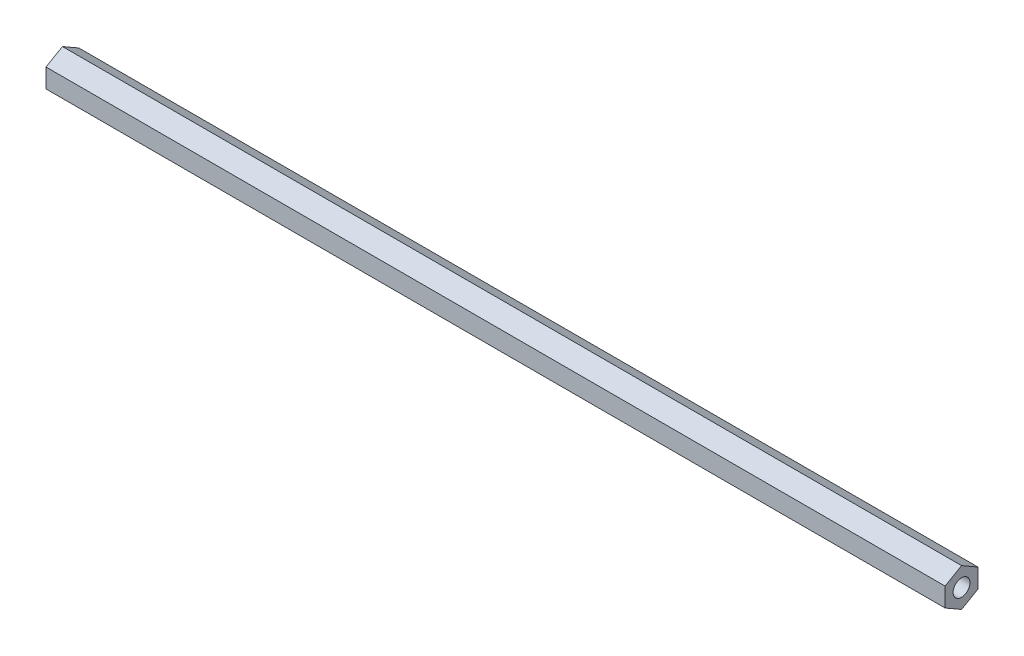
SolidWorks part; units mm, degrees
material "3003 Alloy"
ref_plane "Front Plane" through (0, 0, 0) normal (0, 0, 1) x (1, 0, 0)
ref_plane "Top Plane" through (0, 0, 0) normal (0, 1, 0) x (1, 0, 0)
ref_plane "Right Plane" through (0, 0, 0) normal (1, 0, 0) x (0, 0, -1)
sketch "Sketch1" plane through (0, 0, 0) normal (1, 0, 0) x (0, 0, -1)
  line L1 (0, 7.3323) -> (-6.35, 3.6662)
  line L2 (-6.35, 3.6662) -> (-6.35, -3.6662)
  line L3 (-6.35, -3.6662) -> (0, -7.3323)
  line L4 (0, -7.3323) -> (6.35, -3.6662)
  line L5 (6.35, -3.6662) -> (6.35, 3.6662)
  line L6 (6.35, 3.6662) -> (0, 7.3323)
  circle A0 centre (0, 0) radius 6.35 construction
  dimension "D1" = 12.7
extrude "Boss-Extrude1" add sketch "Sketch1" along normal blind 346.8687
sketch "Sketch2" plane through (346.8687, 0, 0) normal (1, 0, 0) x (0, 0, -1)
  circle A0 centre (0, 0) radius 3.2639
  dimension "D1" = 6.5278
extrude "Cut-Extrude1" cut sketch "Sketch2" against normal blind 12.7
sketch "Sketch3" plane through (0, 0, 0) normal (-1, 0, 0) x (0, 0, 1)
  circle A0 centre (0, 0) radius 3.2639
  dimension "D1" = 6.5278
extrude "Cut-Extrude2" cut sketch "Sketch3" against normal blind 12.7
